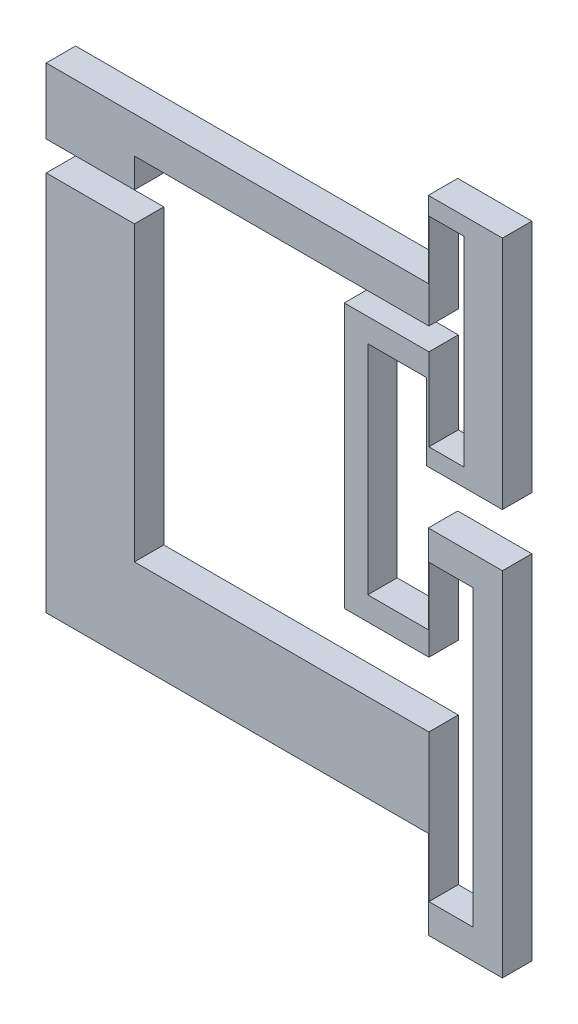
SolidWorks part; units mm, degrees
ref_plane "Front Plane" through (0, 0, 0) normal (0, 0, 1) x (1, 0, 0)
ref_plane "Top Plane" through (0, 0, 0) normal (0, 1, 0) x (1, 0, 0)
ref_plane "Right Plane" through (0, 0, 0) normal (1, 0, 0) x (0, 0, -1)
sketch "Sketch1" plane through (0, 0, 0) normal (0, 0, 1) x (1, 0, 0)
  line L0 (0, 0) -> (0, 64.8)
  line L4 (15, 15) -> (15, 64.8)
  line L5 (15, 64.8) -> (0, 64.8)
  line L6 (0, 69.8) -> (0, 81)
  line L7 (0, 81) -> (65, 81)
  line L8 (65.1, 81) -> (65.1, 74.8)
  line L9 (65.1, 74.8) -> (15, 74.8)
  line L10 (15, 74.8) -> (15, 69.8)
  line L11 (15, 69.8) -> (0, 69.8)
  line L12 (15, 15) -> (65.1, 15)
  line L20 (72.6, -10) -> (72.6, 40)
  line L24 (77.6, 45) -> (77.6, -15)
  line L32 (50.7, 26) -> (50.7, 71)
  line L33 (50.7, 71) -> (65.1, 71)
  line L36 (54.7, 67) -> (54.7, 30)
  line L41 (71.1, 91) -> (65.1, 91)
  line L44 (77.6, 94) -> (77.6, 54)
  line L47 (65.1, 81) -> (65.1, 91)
  line L48 (65, 81) -> (65, 94)
  line L49 (65, 94) -> (77.6, 94)
  line L55 (65.1, 71) -> (65.1, 67)
  line L78 (65.1, 57) -> (71.1, 57)
  line L82 (54.7, 67) -> (64.7, 67)
  line L83 (65.1, 67) -> (65.1, 57)
  line L84 (77.6, 54) -> (64.7, 54)
  line L85 (64.7, 54) -> (64.7, 67)
  line L86 (50.7, 26) -> (65.1, 26)
  line L87 (65.1, 26) -> (65.1, 35)
  line L88 (65, 30) -> (54.7, 30)
  line L89 (77.6, 45) -> (65, 45)
  line L91 (65.1, 40) -> (72.6, 40)
  line L92 (65.1, 35) -> (65.1, 40)
  line L97 (77.6, -15) -> (65, -15)
  line L98 (65, -15) -> (65, -10)
  line L100 (65, -10) -> (65, 0)
  line L101 (72.6, -10) -> (65.1, -10)
  line L105 (0, 0) -> (65, 0)
  line L108 (71.1, 91) -> (71.1, 57)
  line L109 (65, 45) -> (65, 30)
  line L110 (65.1, 15) -> (65.1, -10)
  dimension "D3" = 4
  dimension "D4" = 0.1
  dimension "D5" = 10
  dimension "D6" = 10
  dimension "D7" = 0.4
  dimension "D12" = 6.2
  dimension "D13" = 65
  dimension "D15" = 6.2
  dimension "D10" = 49.8
  dimension "D11" = 60
  dimension "D16" = 7.5
  dimension "D14" = 5
  dimension "D17" = 7.5
  dimension "D19" = 5
  dimension "D21" = 15
  dimension "D24" = 65
  dimension "D25" = 11.2
  dimension "D22" = 15
  dimension "D18" = 5
  dimension "D26" = 40
  dimension "D27" = 6
  dimension "D28" = 6
  dimension "D29" = 3
  dimension "D30" = 3
  dimension "D31" = 45
  dimension "D9" = 4
  dimension "D32" = 4
  dimension "D33" = 10
  dimension "D34" = 10
  dimension "D20" = 10
  dimension "D8" = 0.1
  dimension "D23" = 0.1
extrude "Boss-Extrude1" add sketch "Sketch1" along normal blind 5
equation "\"A.L\"= 0.06m"
equation "\"A.h\"= 0.005m"
equation "\"A.d\"= 0.003m"
equation "\"A.delta\"= 45.0001"
equation "\"A.w\"= 0.02m"
equation "\"A.v\"= 0.03m"
equation "\"B.L\"= 0.04m"
equation "\"B.h\"= 0.003m"
equation "\"C.h\"= 0.0062m"
equation "\"C.d\"= 0.003m"
equation "\"C.L\"= 0.05m"
equation "\"C.wmax\"= 0.005m"
equation "\"a_h\"= 0.0001m"
equation "\"a_d\"= 0.003m"
equation "\"a_L\"= 0.01m"
equation "\"b_h\"= 0.0004m"
equation "\"b_d\"= 0.003m"
equation "\"b_L\"= 0.01m"
equation "\"c_h\"= 0.0001m"
equation "\"c_d\"= 0.003m"
equation "\"c_L\"= 0.01m"
equation "\"S.h\"= 0.015m"
equation "\"S.L\"= 0.0579m"
equation "\"D4@Sketch1\"=\"c_h\""
equation "\"D5@Sketch1\"=\"c_L\""
equation "\"d_h\"= 0.0001m"
equation "\"d_L\"= 0.01m"
equation "\"d_d\"= 0.003m"
equation "\"D6@Sketch1\"=\"b_L\""
equation "\"D7@Sketch1\"=\"b_h\""
equation "\"D13@Sketch1\"=\"C.L\"+\"S.h\""
equation "\"D15@Sketch1\"=\"C.h\""
equation "\"A.t\"= 0.005m"
equation "\"A.s\"= 0.0075m"
equation "\"D11@Sketch1\"=\"A.L\""
equation "\"D16@Sketch1\"=\"A.s\""
equation "\"D17@Sketch1\"=\"A.s\""
equation "\"D19@Sketch1\"=\"A.t\""
equation "\"D21@Sketch1\"=\"S.h\""
equation "\"D24@Sketch1\"=\"C.L\"+\"S.h\""
equation "\"D25@Sketch1\"=\"C.h\"+\"C.wmax\""
equation "\"D22@Sketch1\"=\"S.h\""
equation "\"D18@Sketch1\"=\"A.t\""
equation "\"B.t\"= 0.003m"
equation "\"B.s\"= 0.006m"
equation "\"D26@Sketch1\"=\"B.L\""
equation "\"D27@Sketch1\"=\"B.s\""
equation "\"D28@Sketch1\"=\"B.s\""
equation "\"D29@Sketch1\"=\"B.t\""
equation "\"D30@Sketch1\"=\"B.t\""
equation "\"D14@Sketch1\"=\"A.h\""
equation "\"D.L\"= 0.045m"
equation "\"D.h\"= 0.004m"
equation "\"D.s\"= 0.01m"
equation "\"D.t\"= 0.004m"
equation "\"D31@Sketch1\"=\"D.L\""
equation "\"D3@Sketch1\"=\"D.h\""
equation "\"D9@Sketch1\"=\"D.t\""
equation "\"D33@Sketch1\"=\"a_L\""
equation "\"D34@Sketch1\"=\"D.s\""
equation "\"D32@Sketch1\"=\"D.t\""
equation "\"D20@Sketch1\"=\"d_L\""
equation "\"D10@Sketch1\"=\"S.L\"-\"C.wmax\"-\"C.h\"/2"
equation "\"D8@Sketch1\"=\"d_h\""
equation "\"D23@Sketch1\"=\"d_h\""
